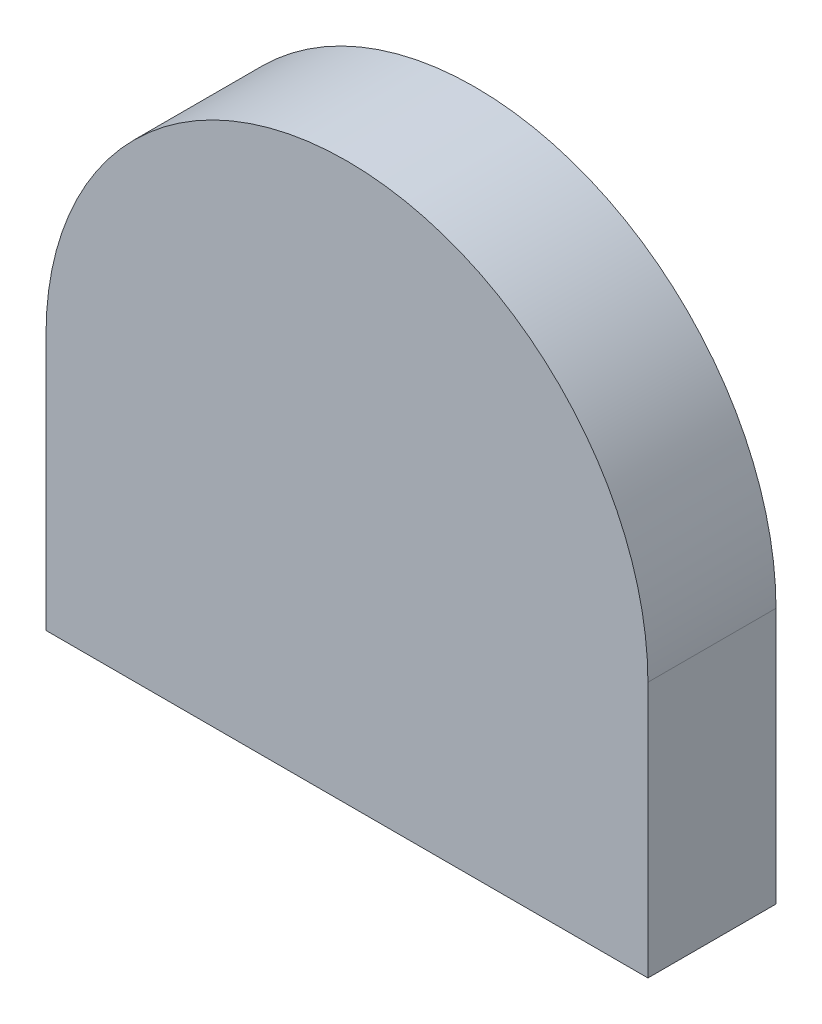
SolidWorks part; units mm, degrees
ref_plane "Płaszczyzna przednia" through (0, 0, 0) normal (0, 0, 1) x (1, 0, 0)
ref_plane "Płaszczyzna górna" through (0, 0, 0) normal (0, 1, 0) x (1, 0, 0)
ref_plane "Płaszczyzna prawa" through (0, 0, 0) normal (1, 0, 0) x (0, 0, -1)
sketch "Szkic1" plane through (0, 0, 0) normal (0, 0, 1) x (1, 0, 0)
  line L1 (0, 0) -> (47, 0)
  line L2 (0, 0) -> (0, 20)
  line L3 (0, 20) -> (47, 20) construction
  line L4 (47, 0) -> (47, 20)
  arc A0 (0, 20) -> (47, 20) centre (23.5, 20) cw
  dimension "D1" = 47
  dimension "D2" = 20
extrude "Dodanie-wyciągnięcie1" add sketch "Szkic1" along normal blind 10
